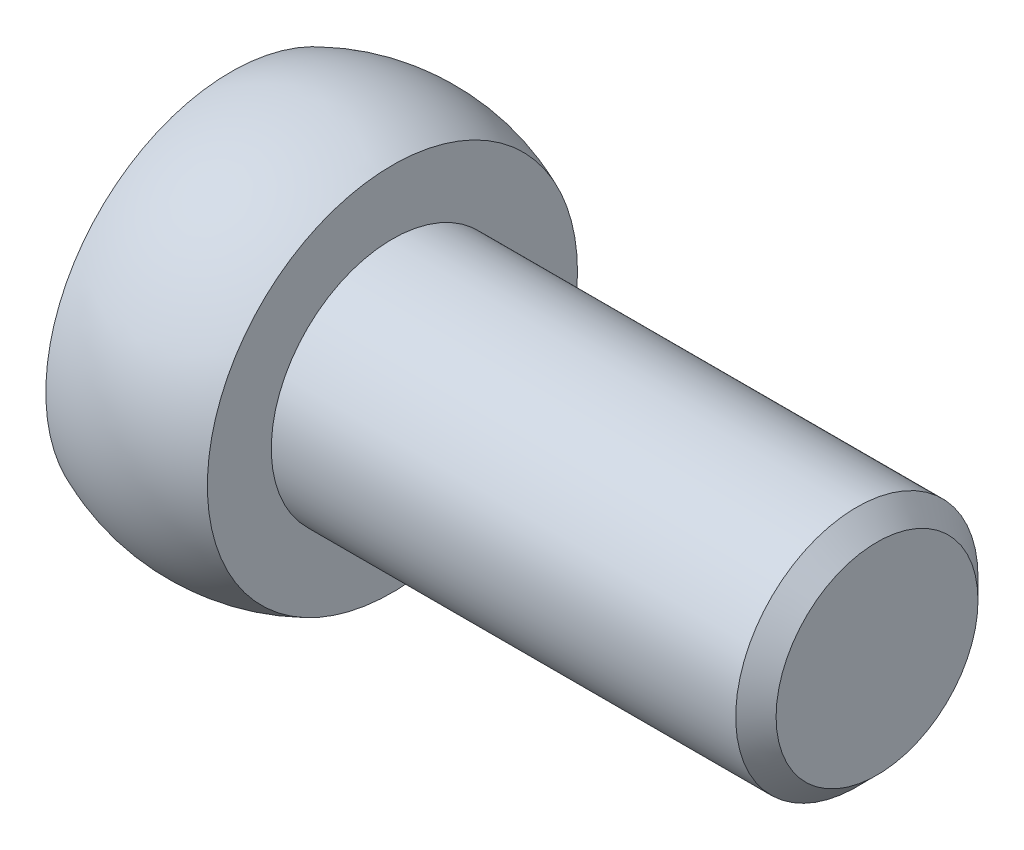
SolidWorks part; units mm, degrees
ref_plane "Спереди" through (0, 0, 0) normal (0, 0, 1) x (1, 0, 0)
ref_plane "Сверху" through (0, 0, 0) normal (0, 1, 0) x (1, 0, 0)
ref_plane "Справа" through (0, 0, 0) normal (1, 0, 0) x (0, 0, -1)
sketch "Эскиз1" plane through (0, 0, 0) normal (0, 0, 1) x (1, 0, 0)
  line L0 (0, 0) -> (0, 4.5826)
  line L1 (0, 0) -> (-1.604, 0) construction
  line L2 (4, 4.5826) -> (4, 3)
  line L3 (4, 3) -> (15.5, 3)
  line L4 (16, 2.5) -> (16, 0)
  line L5 (16, 0) -> (0, 0)
  line L6 (3, 5) -> (0, 5) construction
  line L7 (15.5, 3) -> (16, 2.5)
  arc A0 (0, 4.5826) -> (4, 4.5826) centre (2, 0) cw
  point P6 (16, 3)
  dimension "D5" = 5
  dimension "D6" = 2
  dimension "D1" = 16
  dimension "D2" = 6
  dimension "D3" = 4
  dimension "D4" = 5
  dimension "D7" = 0.5
  dimension "D8" = 45
revolve "Повернуть1" add sketch "Эскиз1" angle 360 about L1
